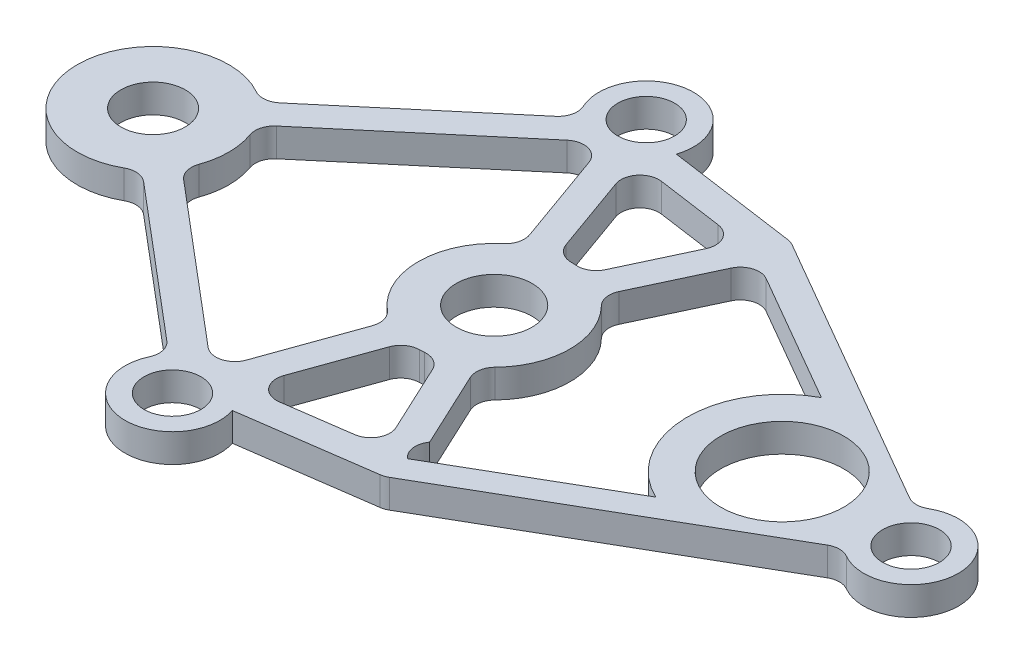
SolidWorks part; units mm, degrees
material "1060 Alloy"
ref_plane "Front" through (0, 0, 0) normal (0, 0, 1) x (1, 0, 0)
ref_plane "Top" through (0, 0, 0) normal (0, 1, 0) x (1, 0, 0)
ref_plane "Right" through (0, 0, 0) normal (1, 0, 0) x (0, 0, -1)
sketch "草图1" plane through (0, 0, 0) normal (0, 1, 0) x (1, 0, 0)
  line L0 (0, 0) -> (-18, 0) construction
  line L1 (0, 0) -> (22, 0) construction
  line L2 (22, 0) -> (4.6795, 10) construction
  line L4 (22, 0) -> (-4.4758, 12.5) construction
  line L5 (0, 0) -> (15.2, 0) construction
  line L6 (0.1065, -1.9972) -> (0.0924, -1.9669)
  line L7 (0.0811, -1.9984) -> (0.0924, -1.9669)
  line L8 (19.75, 2.1651) -> (5.0965, 10.6253)
  line L9 (4.7364, 10.7494) -> (-2.1019, 11.7159)
  line L10 (2.2314, 9.5886) -> (-1.2565, 10.0815)
  line L11 (4.9285, 10.7223) -> (-3.2584, 11.8794) construction
  line L12 (-7.0068, 10.2659) -> (-14.9056, 3.5951)
  line L13 (12.8531, 4.415) -> (5.9562, 8.3969)
  line L14 (4.5504, -7.9547) -> (2.6645, -3.9244)
  line L15 (-2.3379, -8.7543) -> (-0.8728, -4.6624)
  line L16 (2.9972, 8.1746) -> (1.3059, 4.5601)
  line L17 (-5.6221, 9.4721) -> (-13.9377, 2.4491)
  line L18 (-3.2584, 11.8794) -> (-4.5001, 14.0565) construction
  line L19 (-4.0354, -9.0452) -> (-2.285, -4.1568)
  line L20 (-4.5001, 14.0565) -> (-6.1038, 11.0285) construction
  line L21 (-4.9142, 10.0699) -> (-17.5161, -0.573) construction
  line L22 (-6.1038, 11.0285) -> (-18.4839, 0.573) construction
  line L23 (21.625, -0.6495) -> (4.4305, 9.2777) construction
  line L24 (22.375, 0.6495) -> (4.9285, 10.7223) construction
  line L25 (-5.6221, -9.4721) -> (-13.9377, -2.4491)
  line L27 (-4.4515, 10.9435) -> (-4.9142, 10.0699) construction
  line L28 (2.9972, -8.1746) -> (1.3059, -4.5601)
  line L29 (4.4305, 9.2777) -> (-4.1969, 10.4971) construction
  line L30 (13.0261, -4.5027) -> (4.7214, -9.2974)
  line L31 (-4.0354, 9.0452) -> (-2.285, 4.1568)
  line L32 (-7.0068, -10.2659) -> (-14.9056, -3.5951)
  line L33 (-2.3379, 8.7543) -> (-0.8728, 4.6624)
  line L34 (2.2314, -9.5886) -> (-1.2565, -10.0815)
  line L35 (4.5504, 7.9547) -> (2.6645, 3.9244)
  line L38 (4.7364, -10.7494) -> (-2.1019, -11.7159)
  line L39 (19.75, -2.1651) -> (5.0965, -10.6253)
  line L41 (-4.1969, 10.4971) -> (-4.4515, 10.9435) construction
  line L42 (-3.7277, 11.1883) -> (-4.4758, 12.5) construction
  line L43 (-4.4758, 12.5) -> (-5.509, 10.5492) construction
  line L44 (4.6795, 10) -> (-3.7277, 11.1883) construction
  line L45 (-5.509, 10.5492) -> (-18, 0) construction
  circle A0 centre (0, 0) radius 2
  arc A1 (0.3201, 3.9872) -> (0.0549, 3.9996) centre (0, 0) ccw
  circle A2 centre (-18, 0) radius 1.7
  arc A3 (-16.0406, 3.4872) -> (-16.0406, -3.4872) centre (-18, 0) ccw
  circle A4 centre (22, 0) radius 1.5
  arc A5 (20.75, -2.1651) -> (20.75, 2.1651) centre (22, 0) ccw
  arc A7 (-2.5812, 3.0557) -> (-2.5812, -3.0557) centre (0, 0) ccw
  arc A8 (-2.1019, 11.7159) -> (-6.7446, 11.4499) centre (-4.4758, 12.5) ccw
  circle A9 centre (-4.4758, 12.5) radius 1.5
  arc A10 (19.75, 2.1651) -> (20.75, 2.1651) centre (20.25, 3.0311) ccw
  arc A12 (-13.9377, 2.4491) -> (-14.234, 1.3481) centre (-13.2925, 1.6851) ccw
  arc A13 (-14.9056, 3.5951) -> (-16.0406, 3.4872) centre (-15.5508, 4.3591) cw
  arc A14 (-7.0068, 10.2659) -> (-6.7446, 11.4499) centre (-7.6521, 11.0299) ccw
  arc A15 (-2.285, 4.1568) -> (-2.5812, 3.0557) centre (-3.2265, 3.8197) cw
  arc A16 (2.8562, 2.8004) -> (2.6645, 3.9244) centre (3.5702, 3.5005) cw
  arc A17 (0.3201, 3.9872) -> (1.3059, 4.5601) centre (0.4001, 4.984) ccw
  arc A18 (-0.8728, 4.6624) -> (0.0549, 3.9996) centre (0.0687, 4.9995) ccw
  arc A19 (4.5504, 7.9547) -> (5.9562, 8.3969) centre (5.4562, 7.5309) cw
  arc A20 (5.0965, 10.6253) -> (4.7364, 10.7494) centre (4.5965, 9.7592) ccw
  arc A21 (2.2314, 9.5886) -> (2.9972, 8.1746) centre (2.0915, 8.5984) cw
  arc A22 (-1.2565, 10.0815) -> (-2.3379, 8.7543) centre (-1.3965, 9.0914) ccw
  arc A23 (-4.0354, 9.0452) -> (-5.6221, 9.4721) centre (-4.9768, 8.7081) ccw
  arc A24 (2.8562, -2.8004) -> (2.8562, 2.8004) centre (0, 0) ccw
  arc A25 (-14.234, -1.3481) -> (-14.234, 1.3481) centre (-18, 0) ccw
  arc A26 (-4.0354, -9.0452) -> (-5.6221, -9.4721) centre (-4.9768, -8.7081) cw
  arc A27 (-1.2565, -10.0815) -> (-2.3379, -8.7543) centre (-1.3965, -9.0914) cw
  arc A28 (2.2314, -9.5886) -> (2.9972, -8.1746) centre (2.0915, -8.5984) ccw
  arc A29 (5.0965, -10.6253) -> (4.7364, -10.7494) centre (4.5965, -9.7592) cw
  arc A30 (4.5504, -7.9547) -> (4.7214, -9.2974) centre (5.3662, -8.5331) ccw
  arc A31 (-0.8728, -4.6624) -> (0.0549, -3.9996) centre (0.0687, -4.9995) cw
  arc A32 (0.3201, -3.9872) -> (1.3059, -4.5601) centre (0.4001, -4.984) cw
  arc A33 (2.8562, -2.8004) -> (2.6645, -3.9244) centre (3.5702, -3.5005) ccw
  arc A34 (-2.285, -4.1568) -> (-2.5812, -3.0557) centre (-3.2265, -3.8197) ccw
  arc A35 (-7.0068, -10.2659) -> (-6.7446, -11.4499) centre (-7.6521, -11.0299) cw
  arc A36 (-14.9056, -3.5951) -> (-16.0406, -3.4872) centre (-15.5508, -4.3591) ccw
  arc A37 (-13.9377, -2.4491) -> (-14.234, -1.3481) centre (-13.2925, -1.6851) cw
  arc A38 (19.75, -2.1651) -> (20.75, -2.1651) centre (20.25, -3.0311) cw
  circle A39 centre (-4.4758, -12.5) radius 1.5
  arc A40 (-2.1019, -11.7159) -> (-6.7446, -11.4499) centre (-4.4758, -12.5) cw
  arc A41 (0.3201, -3.9872) -> (0.0549, -3.9996) centre (0, 0) cw
  circle A42 centre (15.2, 0) radius 3.25
  arc A45 (12.8531, 4.415) -> (13.0261, -4.5027) centre (15.2, 0) ccw
  point P53 (-2.0306, 3.4463)
  point P79 (-2.0306, -3.4463)
  dimension "D1" = 30
  dimension "D2" = 0.75
  dimension "D4" = 1
  dimension "D6" = 15.2
  dimension "D7" = 3.4
  dimension "D8" = 5
  dimension "D9" = 6.5
  dimension "D5" = 25.273
  dimension "D3" = 0.75
extrude "凸台-拉伸1" add sketch "草图1" along normal blind 1.5 contours A40 L38 A29 L39 A38 A5 A10 L8 A20 L9 A8 A14 L12 A13 A3 A36 L32 A35 A41 A32 L28 A28 L34 A27 L15 A31 L25 A37 A25 A12 L17 A23 L31 A15 A7 A34 L19 A26 A0 A2 A4 A9 A22
